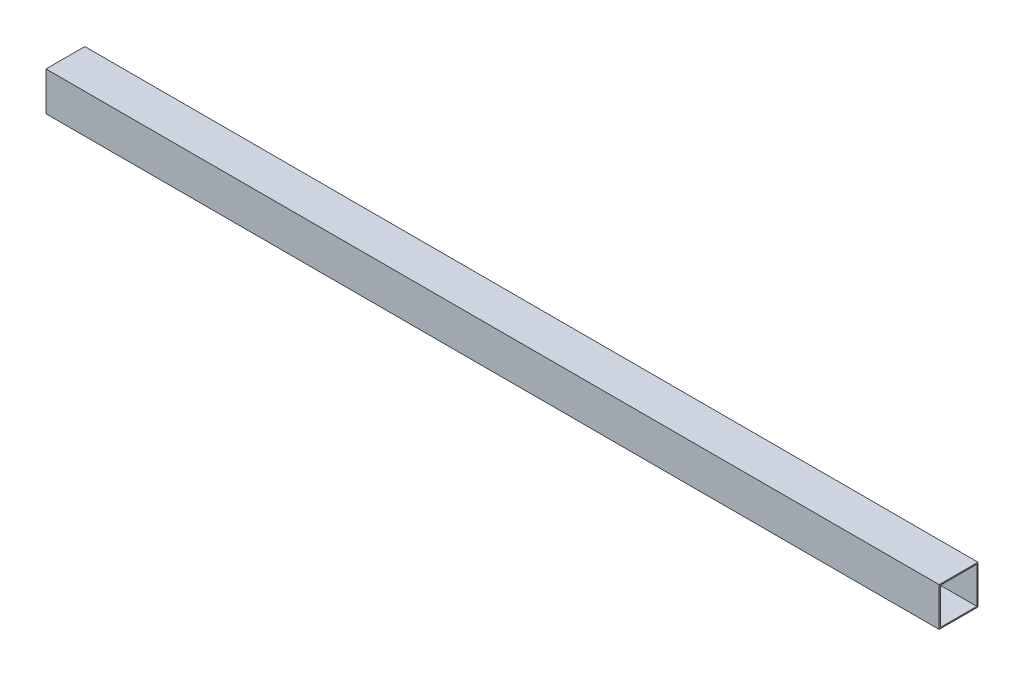
SolidWorks part; units mm, degrees
material "1060 Alloy"
ref_plane "Front Plane" through (0, 0, 0) normal (0, 0, 1) x (1, 0, 0)
ref_plane "Top Plane" through (0, 0, 0) normal (0, 1, 0) x (1, 0, 0)
ref_plane "Right Plane" through (0, 0, 0) normal (1, 0, 0) x (0, 0, -1)
sketch "Sketch1" plane through (0, 0, 0) normal (1, 0, 0) x (0, 0, -1)
  line L1 (0, 0) -> (25.4, 0)
  line L2 (0, 0) -> (0, 25.4)
  line L3 (0, 25.4) -> (25.4, 25.4)
  line L4 (25.4, 0) -> (25.4, 25.4)
  dimension "D1" = 25.4
  dimension "D2" = 25.4
extrude "Extrude-Thin1" add sketch "Sketch1" along normal blind 584.2 thin thin type one direction reverse wall 0.762
